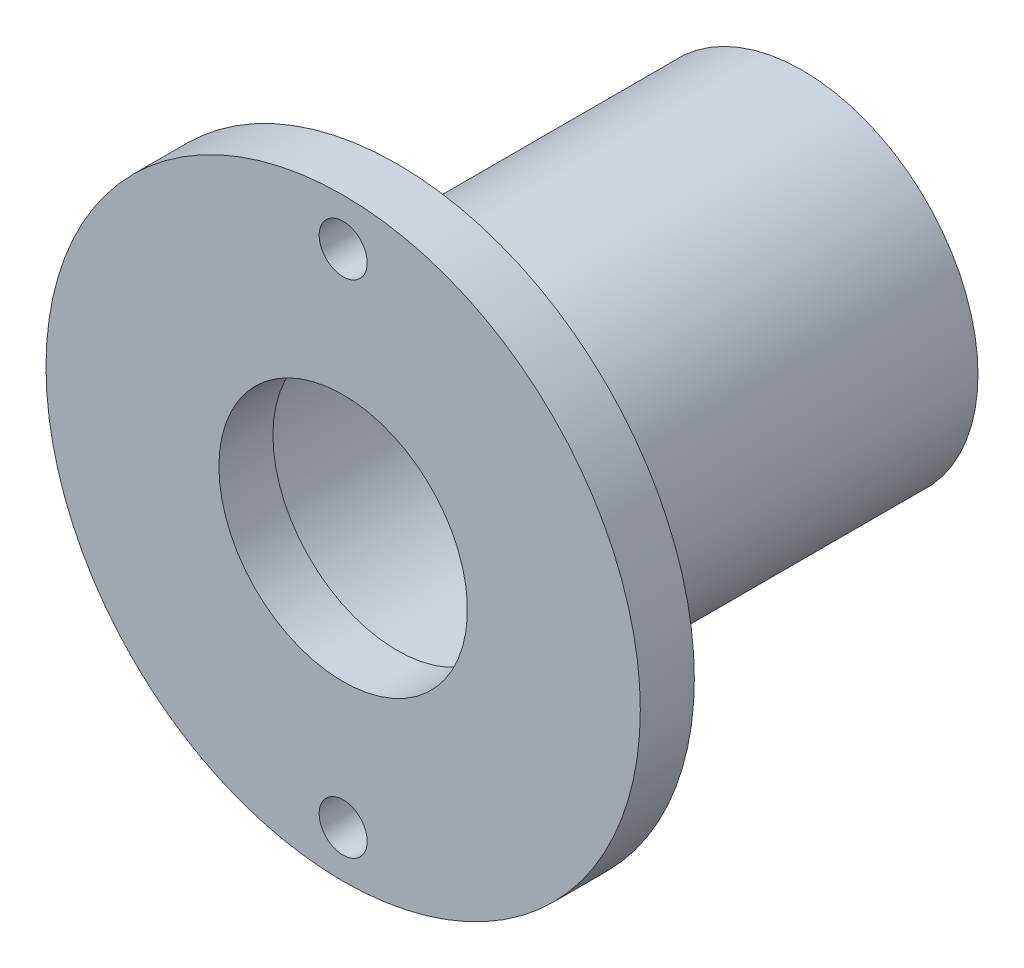
SolidWorks part; units mm, degrees
material "6061-T6 (SS)"
ref_plane "Front Plane" through (0, 0, 0) normal (0, 0, 1) x (1, 0, 0)
ref_plane "Top Plane" through (0, 0, 0) normal (0, 1, 0) x (1, 0, 0)
ref_plane "Right Plane" through (0, 0, 0) normal (1, 0, 0) x (0, 0, -1)
sketch "Sketch1" plane through (0, 0, 0) normal (1, 0, 0) x (0, 0, -1)
  line L0 (0, 0) -> (0, -26.8379) construction
  line L1 (0, 0) -> (-30.0063, 0) construction
  line L2 (0, 11) -> (0, 4.6)
  line L3 (0, 4.6) -> (2, 4.6)
  line L4 (2, 4.6) -> (2, 5.275)
  line L5 (2, 5.275) -> (8, 5.275)
  line L6 (8, 5.275) -> (8, 5.5)
  line L7 (8, 5.5) -> (17, 5.5)
  line L8 (17, 5.5) -> (17, 6.5)
  line L9 (17, 6.5) -> (2, 6.5)
  line L10 (2, 6.5) -> (2, 11)
  line L11 (2, 11) -> (0, 11)
  dimension "D1" = 2
  dimension "D2" = 10.55
  dimension "D3" = 9.2
  dimension "D4" = 22
  dimension "D5" = 11
  dimension "D6" = 6
  dimension "D7" = 1
  dimension "D8" = 15
revolve "Revolve1" add sketch "Sketch1" angle 360 about L1
sketch "Sketch2" plane through (0, 0, -2) normal (0, 0, -1) x (-1, 0, 0)
  line L0 (0, 9.2718) -> (0, -9.2718) construction
  point P2 (0, 0)
  dimension "D1" = 18.5436
hole_wizard "#0 Clearance Hole1" positions "Sketch4" profile "Sketch3" hole size "#0" standard "Ansi Inch"
sketch "Sketch4" plane through (0, 0, -2) normal (0, 0, -1) x (-1, 0, 0)
  point P0 (0, 9.2718)
  point P1 (0, -9.2718)
sketch "Sketch3" plane through (0, 9.2718, -2) normal (1, 0, 0) x (0, 1, 0)
  line L0 (0, 0) -> (0, 19.5842)
  line L1 (0, 19.5842) -> (0.889, 19.05)
  line L2 (0.889, 19.05) -> (0.889, 0)
  line L5 (0.889, 0) -> (0, 0)
  line L10 (0, 19.5842) -> (-0.889, 19.05) construction
  line L11 (0, -6.35) -> (0, 107.95) construction
  dimension "Hole Dia." = 1.778
  dimension "Hole Depth" = 19.05
  dimension "Drill Angle" = 118
